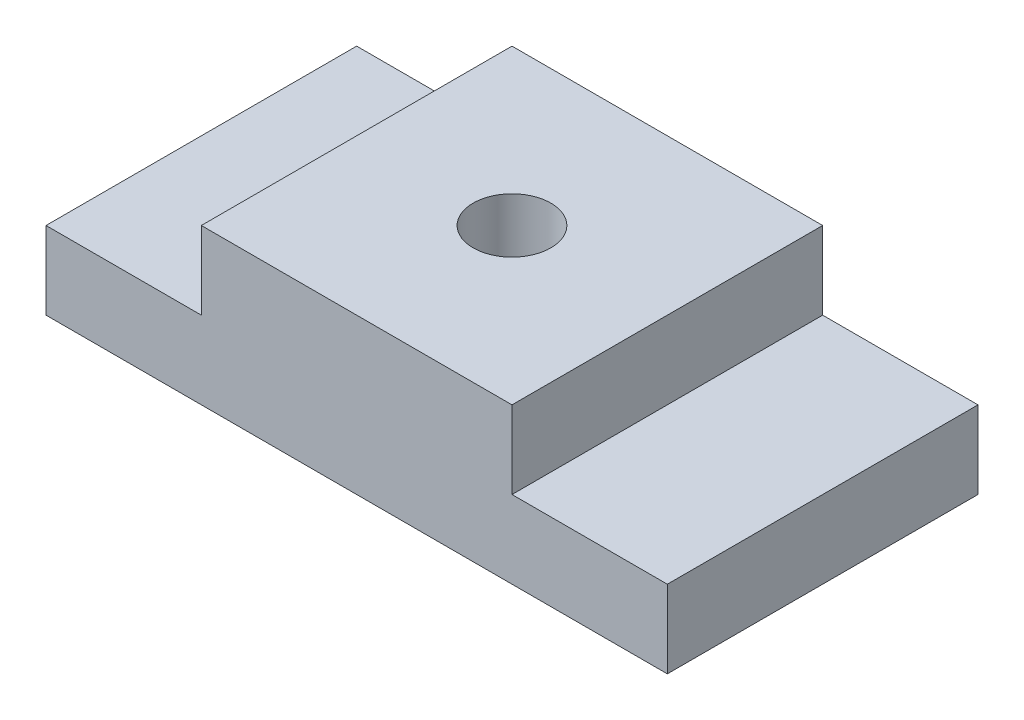
SolidWorks part; units mm, degrees
ref_plane "Front Plane" through (0, 0, 0) normal (0, 0, 1) x (1, 0, 0)
ref_plane "Top Plane" through (0, 0, 0) normal (0, 1, 0) x (1, 0, 0)
ref_plane "Right Plane" through (0, 0, 0) normal (1, 0, 0) x (0, 0, -1)
sketch "Sketch1" plane through (0, 0, 0) normal (0, 1, 0) x (1, 0, 0)
  line L1 (-40, -20) -> (40, -20)
  line L2 (-40, -20) -> (-40, 20)
  line L3 (-40, 20) -> (40, 20)
  line L4 (40, -20) -> (40, 20)
  line L5 (-40, -20) -> (40, 20) construction
  line L6 (-40, 20) -> (40, -20) construction
  point P0 (0, 0)
  dimension "D1" = 40
  dimension "D2" = 80
extrude "Boss-Extrude1" add sketch "Sketch1" along normal blind 10
sketch "Sketch2" plane through (0, 10, 0) normal (0, 1, 0) x (1, 0, 0)
  line L0 (40, 20) -> (-40, 20) construction
  line L1 (-20, -20) -> (20, -20)
  line L2 (-20, -20) -> (-20, 20)
  line L3 (-20, 20) -> (20, 20)
  line L4 (20, -20) -> (20, 20)
  line L5 (-20, -20) -> (20, 20) construction
  line L6 (-20, 20) -> (20, -20) construction
  point P0 (0, 0)
  dimension "D1" = 40
extrude "Boss-Extrude2" add sketch "Sketch2" along normal blind 10
sketch "Sketch3" plane through (0, 20, 0) normal (0, 1, 0) x (1, 0, 0)
  circle A0 centre (0, 0) radius 5
  dimension "D1" = 10
extrude "Cut-Extrude1" cut sketch "Sketch3" against normal blind 10
